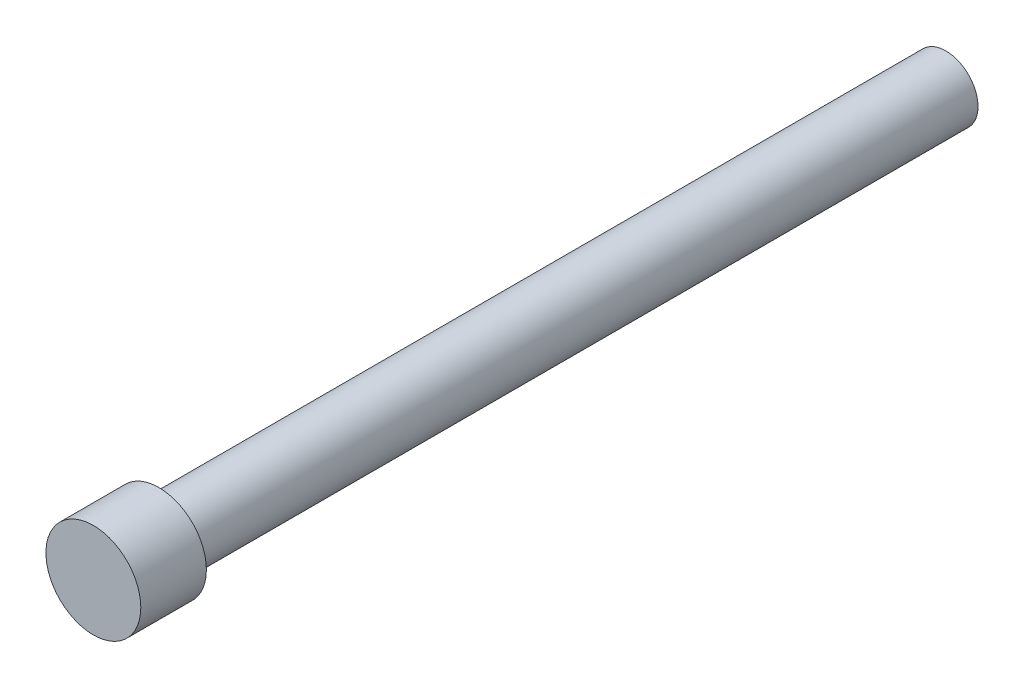
SolidWorks part; units mm, degrees
ref_plane "Alzado" through (0, 0, 0) normal (0, 0, 1) x (1, 0, 0)
ref_plane "Planta" through (0, 0, 0) normal (0, 1, 0) x (1, 0, 0)
ref_plane "Vista lateral" through (0, 0, 0) normal (1, 0, 0) x (0, 0, -1)
sketch "Croquis1" plane through (0, 0, 0) normal (0, 0, 1) x (1, 0, 0)
  circle A0 centre (-17.2735, 7.4418) radius 2.45
extrude "Saliente-Extruir1" add sketch "Croquis1" along normal blind 60
sketch "Croquis2" plane through (0, 0, 60) normal (0, 0, 1) x (1, 0, 0)
  line L0 (-17.2735, 9.8918) -> (-17.2735, 7.4418)
  circle A0 centre (-17.2735, 7.4418) radius 2.45 construction
  circle A1 centre (-17.2735, 7.4418) radius 3.6176
extrude "Saliente-Extruir2" add sketch "Croquis2" along normal blind 5
